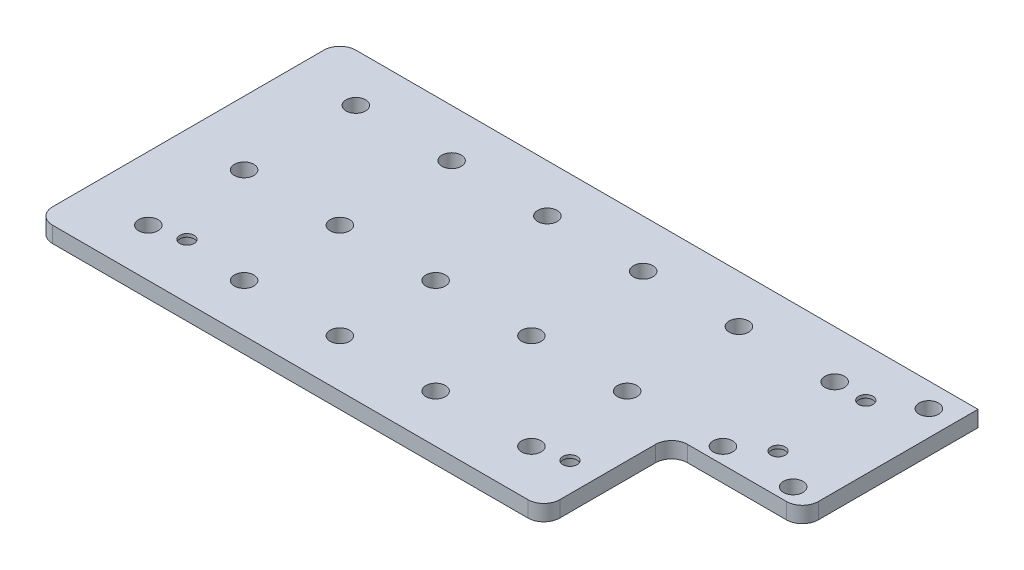
SolidWorks part; units mm, degrees
ref_plane "Front Plane" through (0, 0, 0) normal (0, 0, 1) x (1, 0, 0)
ref_plane "Top Plane" through (0, 0, 0) normal (0, 1, 0) x (1, 0, 0)
ref_plane "Right Plane" through (0, 0, 0) normal (1, 0, 0) x (0, 0, -1)
sketch "Sketch1" plane through (0, 0, 0) normal (0, 1, 0) x (1, 0, 0)
  line L1 (0, 0) -> (199.9, 0)
  line L2 (0, 0) -> (0, -95)
  line L3 (0, -95) -> (199.9, -95)
  line L4 (199.9, 0) -> (199.9, -95)
  dimension "D1" = 199.9
  dimension "D2" = 95
extrude "Boss-Extrude1" add sketch "Sketch1" along normal blind 5
sketch "Sketch2" plane through (0, 0, 0) normal (0, 1, 0) x (1, 0, 0)
  line L0 (0, -77.8) -> (199.9, -77.8) construction
  line L1 (0, 0) -> (0, -95) construction
  line L2 (179.9, 0) -> (179.9, -57.8) construction
  line L3 (199.9, 0) -> (0, 0) construction
  line L4 (0, -95) -> (199.9, -95) construction
  line L5 (199.9, -95) -> (199.9, 0) construction
  line L6 (179.9, -57.8) -> (199.9, -57.8) construction
  line L7 (179.9, -28.9) -> (199.9, -28.9) construction
  point P5 (149.9, -77.8)
  point P17 (29.9, -77.8)
  point P19 (179.9, -42.65)
  point P20 (179.9, -15.15)
  point P22 (69.9, -77.8) [skipped]
  point P24 (109.9, -77.8) [skipped]
  dimension "D1" = 17.2
  dimension "D2" = 20
  dimension "D3" = 37.2
  dimension "D4" = 50
  dimension "D6" = 27.5
  dimension "D5" = 4
hole_wizard "CBORE for M4 SHCS1" positions "Sketch2" profile "Sketch3" counterbore size "M4" standard "ANSI Metric"
sketch "Sketch3" plane through (179.9, 0, 15.15) normal (1, 0, 0) x (0, 0, -1)
  line L0 (0, 0) -> (0, 5)
  line L1 (0, 5) -> (2.25, 5)
  line L3 (2.25, 5) -> (2.25, 4)
  line L4 (4, 4) -> (2.25, 4)
  line L5 (4, 4) -> (4, 0.025)
  line L6 (4, 0.025) -> (4.025, 0)
  line L7 (4.025, 0) -> (0, 0)
  line L8 (-4, 0.025) -> (-4.025, 0) construction
  line L11 (0, -6.35) -> (0, 107.95) construction
  dimension "Thru Hole Dia." = 4.5
  dimension "Thru Hole Depth" = 5
  dimension "C'Bore Dia." = 8
  dimension "C'Bore Depth" = 4
  dimension "Near C'Sink Dia." = 8.05
  dimension "Near C'Sink Angle" = 90
sketch "Sketch4" plane through (0, 5, 0) normal (0, 1, 0) x (1, 0, 0)
  line L0 (0, -15) -> (200.6419, -15) construction
  line L1 (0, 0) -> (0, -95) construction
  line L2 (199.9, 0) -> (0, 0) construction
  point P4 (20, -15)
  point P7 (50, -15)
  point P9 (80, -15)
  point P10 (110, -15)
  point P11 (140, -15)
  point P12 (170, -15)
  dimension "D1" = 15
  dimension "D2" = 20
  dimension "D3" = 6
hole_wizard "Ø6.1 (6.1) Diameter Hole2" positions "Sketch4" profile "Sketch5" hole size "Ø6.1" standard "ANSI Metric" end condition through all
sketch "Sketch5" plane through (170, 5, 15) normal (1, 0, 0) x (0, 0, 1)
  line L0 (0, 0) -> (0, 5)
  line L1 (0, 5) -> (3.05, 5)
  line L2 (3.05, 5) -> (3.05, 0)
  line L5 (3.05, 0) -> (0, 0)
  line L11 (0, -6.35) -> (0, 107.95) construction
  dimension "Thru Hole Dia." = 6.1
  dimension "Thru Hole Depth" = 5
pattern_linear "LPattern1" count 2 spacing 35 along (0, 0, 1) of "Ø6.1 (6.1) Diameter Hole2"
sketch "Sketch6" plane through (0, 5, 0) normal (0, 1, 0) x (1, 0, 0)
  line L1 (199.9, -95) -> (158.9, -95)
  line L2 (199.9, -95) -> (199.9, -55)
  line L3 (199.9, -55) -> (158.9, -55)
  line L4 (158.9, -95) -> (158.9, -55)
  dimension "D1" = 41
  dimension "D2" = 40
extrude "Cut-Extrude1" cut sketch "Sketch6" against normal through all
pattern_linear "LPattern2" count 2 spacing 65 along (0, 0, 1) of "Ø6.1 (6.1) Diameter Hole2"
fillet "Fillet1" radius 5 5 edges at (158.9, 2.5, 55) (199.9, 2.5, 55) (158.9, 2.5, 95) (0, 2.5, 95) (0, 2.5, 0)
sketch "Sketch7" plane through (0, 5, 0) normal (0, 1, 0) x (1, 0, 0)
  line L1 (170, -50) -> (192, -50) construction
  line L2 (192, -7.5) -> (192, -50) construction
  line L3 (199.9, -50) -> (199.9, 0) construction
  point P7 (192, -7.5)
  point P8 (192, -50)
  dimension "D1" = 42.5
  dimension "D2" = 7.9
hole_wizard "Ø6.1 (6.1) Diameter Hole1" positions "Sketch7" profile "Sketch8" hole size "Ø6.1" standard "ANSI Metric" end condition through all
sketch "Sketch8" plane through (192, 5, 50) normal (1, 0, 0) x (0, 0, 1)
  line L0 (0, 0) -> (0, 5)
  line L1 (0, 5) -> (3.05, 5)
  line L2 (3.05, 5) -> (3.05, 0)
  line L5 (3.05, 0) -> (0, 0)
  line L11 (0, -6.35) -> (0, 107.95) construction
  dimension "Thru Hole Dia." = 6.1
  dimension "Thru Hole Depth" = 5
